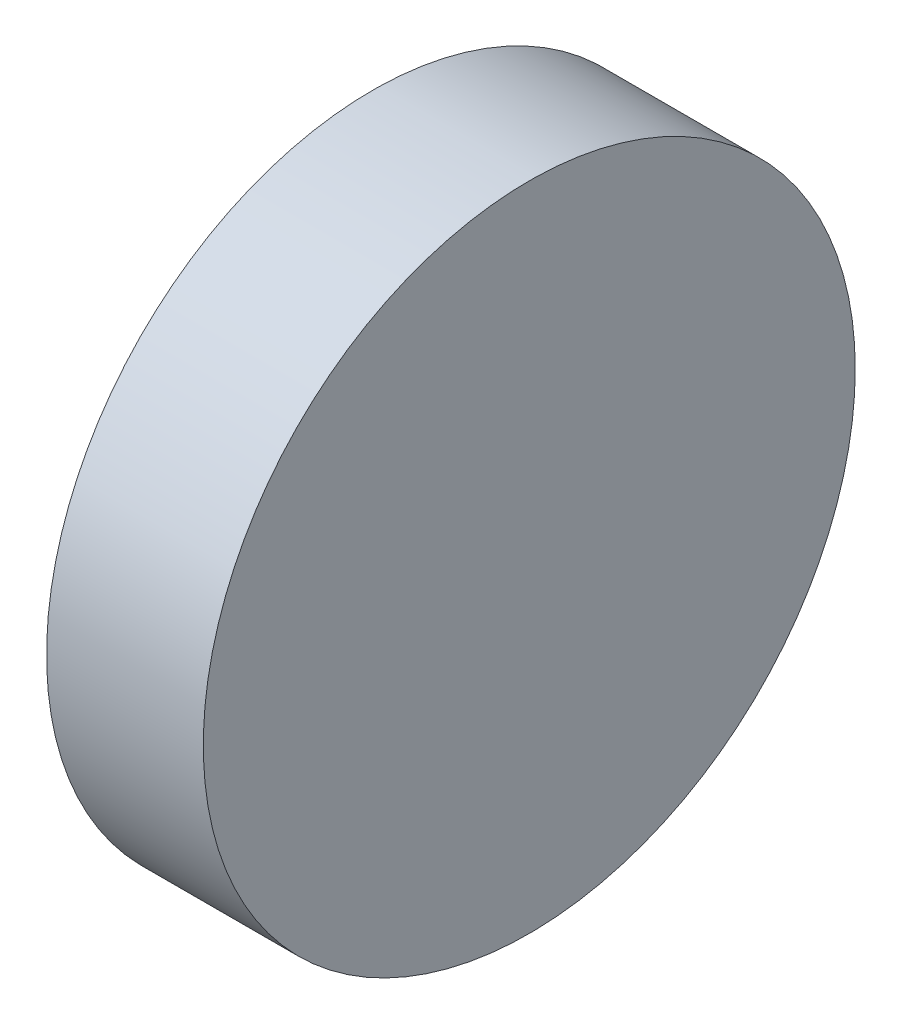
SolidWorks part; units mm, degrees
ref_plane "Front Plane" through (0, 0, 0) normal (0, 0, 1) x (1, 0, 0)
ref_plane "Top Plane" through (0, 0, 0) normal (0, 1, 0) x (1, 0, 0)
ref_plane "Right Plane" through (0, 0, 0) normal (1, 0, 0) x (0, 0, -1)
sketch "Sketch1" plane through (0, 0, 0) normal (1, 0, 0) x (0, 0, -1)
  circle A0 centre (0, 0) radius 41.597
extrude "Boss-Extrude1" add sketch "Sketch1" along normal mid plane 20
